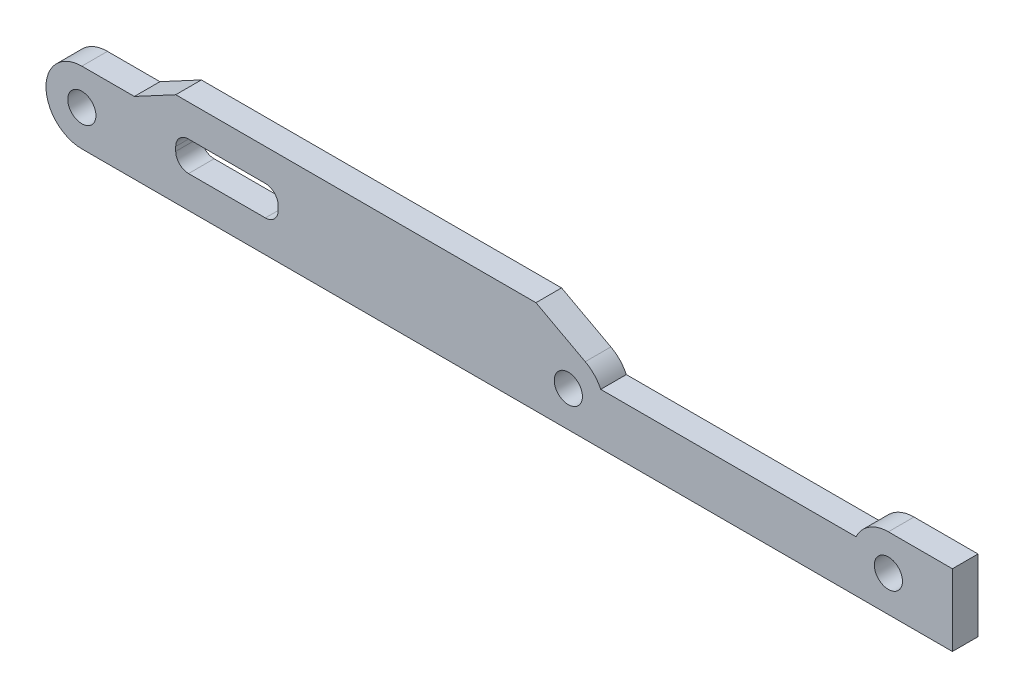
SolidWorks part; units mm, degrees
material "6061-T6 Black anodised"
ref_plane "Front Plane" through (0, 0, 0) normal (0, 0, 1) x (1, 0, 0)
ref_plane "Top Plane" through (0, 0, 0) normal (0, 1, 0) x (1, 0, 0)
ref_plane "Right Plane" through (0, 0, 0) normal (1, 0, 0) x (0, 0, -1)
sketch "Sketch1" plane through (0, 0, 0) normal (0, 0, 1) x (1, 0, 0)
  line L0 (-53.2053, 1.8) -> (-46, 1.8) construction
  line L1 (-57, -4.2) -> (45, -4.2)
  line L2 (-46, -0.45) -> (-34, -0.45)
  line L3 (37.5, 4.2) -> (45, 4.2)
  line L4 (45, -4.2) -> (45, 4.2)
  line L5 (-34, -0.45) -> (-34, 1.8)
  line L6 (-34, 1.8) -> (-3.7947, 1.8) construction
  line L7 (-46, 1.8) -> (-46, -0.45)
  line L8 (-46, 6.8) -> (-3.7947, 6.8)
  line L9 (3.7947, 1.8) -> (33.7053, 1.8)
  line L10 (-3.7947, 6.8) -> (1.9845, 3.7016)
  line L11 (-53.2053, 6.8) -> (-58.4299, 3.9989) construction
  line L12 (-46, 3.05) -> (-34, 3.05)
  line L13 (-34, 3.05) -> (-34, 1.8)
  line L14 (-46, 1.8) -> (-46, 3.05)
  line L15 (-57, 4.2) -> (-50.8496, 4.2)
  line L16 (-50.8496, 4.2) -> (-46, 6.8)
  circle A0 centre (0, 0) radius 1.65
  circle A1 centre (-57, 0) radius 1.65
  circle A2 centre (37.5, 0) radius 1.65
  arc A3 (-57, -4.2) -> (-57, 4.2) centre (-57, 0) cw
  arc A4 (37.5, 4.2) -> (33.7053, 1.8) centre (37.5, 0) ccw
  arc A6 (3.7947, 1.8) -> (1.9845, 3.7016) centre (0, 0) ccw
  dimension "D2" = 37.5
  dimension "D3" = 3.3
  dimension "D1" = 57
  dimension "D4" = 4.2
  dimension "D5" = 7.5
  dimension "D6" = 6
  dimension "D7" = 3.75
  dimension "D8" = 11
  dimension "D9" = 12
  dimension "D10" = 11
  dimension "D11" = 3.5
extrude "Boss-Extrude1" add sketch "Sketch1" along normal blind 3
fillet "Fillet1" radius 1.5 4 edges at (-34, -0.45, 1.5) (-46, -0.45, 1.5) (-34, 3.05, 1.5) (-46, 3.05, 1.5)
